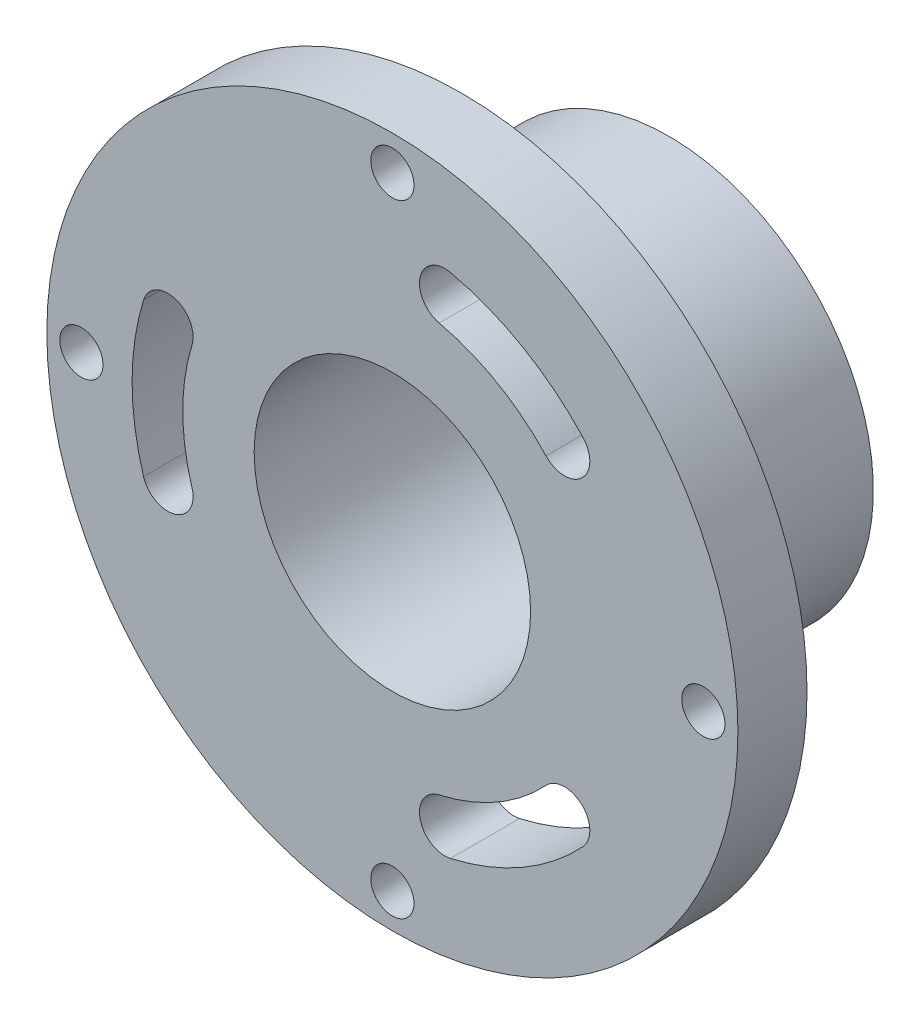
SolidWorks part; units mm, degrees
ref_plane "Front Plane" through (0, 0, 0) normal (0, 0, 1) x (1, 0, 0)
ref_plane "Top Plane" through (0, 0, 0) normal (0, 1, 0) x (1, 0, 0)
ref_plane "Right Plane" through (0, 0, 0) normal (1, 0, 0) x (0, 0, -1)
sketch "Sketch1" plane through (0, 0, 0) normal (0, 0, 1) x (1, 0, 0)
  circle A0 centre (0, 0) radius 31.75
  dimension "D1" = 63.5
extrude "Boss-Extrude1" add sketch "Sketch1" along normal blind 25.4
sketch "Sketch2" plane through (0, 0, 0) normal (0, 0, -1) x (-1, 0, 0)
  circle A0 centre (0, 0) radius 18.796
  dimension "D1" = 37.592
extrude "Cut-Extrude1" cut sketch "Sketch2" against normal offset from surface (19.05 mm away) 19.05 flip side to cut up to plane "Front Plane"
sketch "Sketch3" plane through (0, 0, 0) normal (0, 0, -1) x (-1, 0, 0)
  circle A0 centre (0, 0) radius 12.7
  dimension "D1" = 25.4
extrude "Cut-Extrude2" cut sketch "Sketch3" against normal through all
hole_wizard "#2-56 Tapped Hole1" positions "Sketch8" profile "Sketch7" tap size "#2-56" standard "ANSI Inch"
sketch "Sketch8" plane through (0, 0, 0) normal (0, 0, -1) x (-1, 0, 0)
  point P0 (0, 15.24)
  point P4 (0, -15.24)
  dimension "D1" = 15.24
  dimension "D2" = 15.24
sketch "Sketch7" plane through (0, 15.24, 0) normal (1, 0, 0) x (0, 1, 0)
  line L0 (0, 0) -> (0, 6.2669)
  line L1 (0, 6.2669) -> (0.889, 5.7328)
  line L2 (0.889, 5.7328) -> (0.889, 0)
  line L5 (0.889, 0) -> (0, 0)
  line L10 (0, 6.2669) -> (-0.889, 5.7328) construction
  line L11 (0, -6.35) -> (0, 107.95) construction
  dimension "Tap Drill Dia." = 1.778
  dimension "Tap Drill Depth" = 5.7328
  dimension "Drill Angle" = 118
hole_wizard "5/32 (0.15625) Diameter Hole1" positions "Sketch5" profile "Sketch6" hole size "5/32" standard "ANSI Inch" end condition through all
sketch "Sketch5" plane through (0, 0, 25.4) normal (0, 0, 1) x (1, 0, 0)
  point P0 (0, 28.575)
  point P2 (28.575, 0)
  dimension "D1" = 28.575
  dimension "D2" = 28.575
sketch "Sketch6" plane through (0, 28.575, 25.4) normal (1, 0, 0) x (0, -1, 0)
  line L0 (0, 0) -> (0, 25.4)
  line L1 (0, 25.4) -> (1.9844, 25.4)
  line L2 (1.9844, 25.4) -> (1.9844, 0)
  line L5 (1.9844, 0) -> (0, 0)
  line L11 (0, -6.35) -> (0, 107.95) construction
  dimension "Thru Hole Dia." = 3.9688
  dimension "Thru Hole Depth" = 25.4
mirror "Mirror1" about plane through (0, 0, 0) normal (0, 1, 0) of "5/32 (0.15625) Diameter Hole1"
mirror "Mirror2" about plane through (0, 0, 0) normal (1, 0, 0) of "Mirror1"
sketch "Sketch9" plane through (0, 0, 25.4) normal (0, 0, 1) x (1, 0, 0)
  line L0 (0, 25.1558) -> (0, 0) construction
  line L1 (0, 0) -> (23.0699, 39.9583) construction
  arc A0 (4.8183, 21.0455) -> (15.8168, 14.6955) centre (0, 0) cw construction
  arc A1 (17.5207, 16.2786) -> (5.3373, 23.3127) centre (0, 0) ccw
  arc A2 (14.1129, 13.1124) -> (4.2992, 18.7783) centre (0, 0) ccw
  arc A3 (14.1129, 13.1124) -> (17.5207, 16.2786) centre (15.8168, 14.6955) ccw
  arc A4 (5.3373, 23.3127) -> (4.2992, 18.7783) centre (4.8183, 21.0455) ccw
  point P4 (10.795, 18.6975)
  dimension "D1" = 30
  dimension "D2" = 6.35
  dimension "D3" = 21.59
extrude "Cut-Extrude3" cut sketch "Sketch9" against normal through all
pattern_circular "CirPattern1" count 3 over 360 about axis through (0, 0, 0) along (0, 0, 1) of "Cut-Extrude3"
sketch "Sketch10" plane through (0, 0, 0) normal (0, 0, -1) x (-1, 0, 0)
  circle A0 centre (0, 0) radius 10.16
  circle A1 centre (0, 0) radius 7.9375
  dimension "D1" = 15.875
  dimension "D2" = 20.32
extrude "Cut-Extrude4" cut sketch "Sketch10" against normal blind 3.175
equation "\"D2@Sketch8\"=\"D1@Sketch8\""
equation "\"D2@Sketch5\"=\"D1@Sketch5\""
